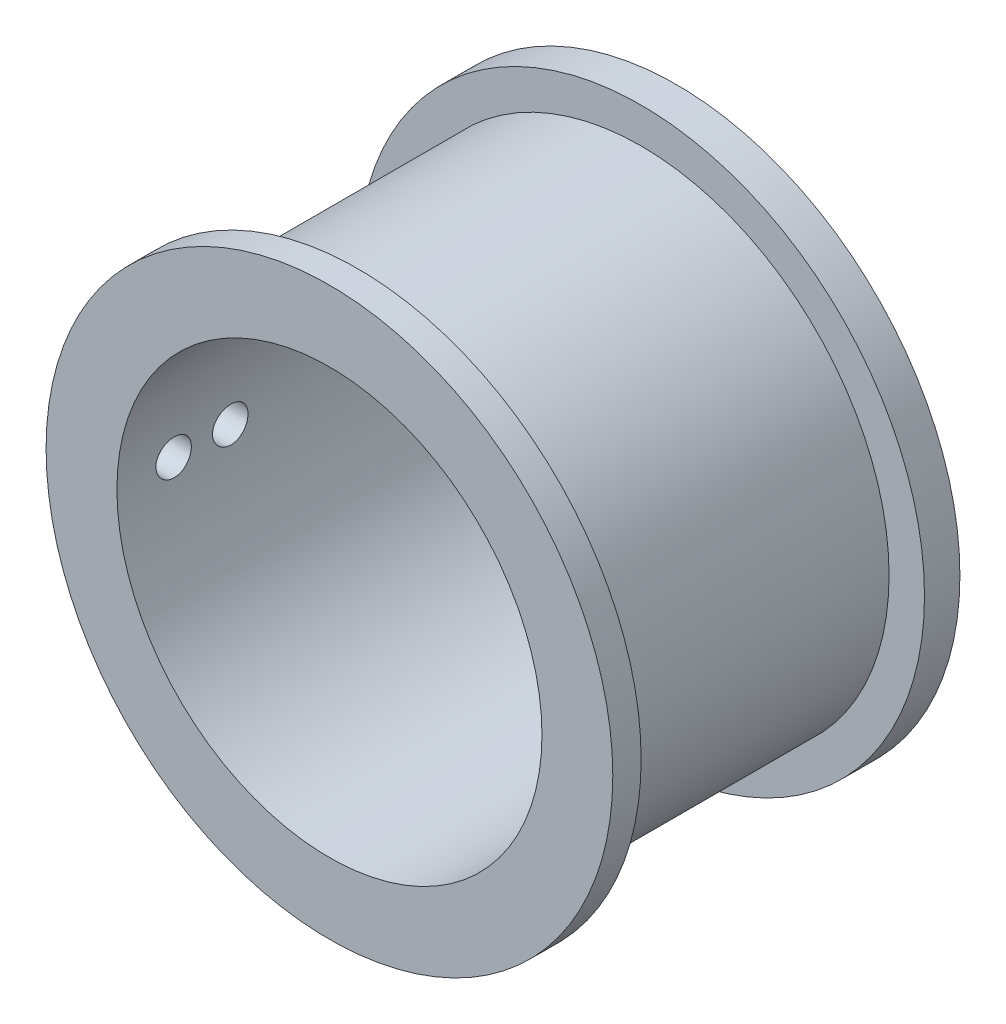
SolidWorks part; units mm, degrees
ref_plane "Front Plane" through (0, 0, 0) normal (0, 0, 1) x (1, 0, 0)
ref_plane "Top Plane" through (0, 0, 0) normal (0, 1, 0) x (1, 0, 0)
ref_plane "Right Plane" through (0, 0, 0) normal (1, 0, 0) x (0, 0, -1)
sketch "Sketch1" plane through (0, 0, 0) normal (0, 0, 1) x (1, 0, 0)
  circle A0 centre (0, 0) radius 25.4
  circle A1 centre (0, 0) radius 8.001 construction
  circle A2 centre (0, -8.001) radius 1.7
  circle A3 centre (0, 8.001) radius 1.7
  circle A4 centre (-6.9291, 4.0005) radius 1.7
  arc A5 (0, 8.001) -> (-6.9291, 4.0005) centre (0, 0) ccw construction
  circle A6 centre (-6.9291, -4.0005) radius 1.7
  circle A7 centre (6.9291, -4.0005) radius 1.7
  circle A8 centre (6.9291, 4.0005) radius 1.7
  dimension "D1" = 50.8
  dimension "D2" = 16.002
  dimension "D9" = 3.4
  dimension "D5" = 60
extrude "Boss-Extrude1" add sketch "Sketch1" along normal blind 3.175
sketch "Sketch4" plane through (0, 0, 3.175) normal (0, 0, 1) x (1, 0, 0)
  circle A0 centre (0, 0) radius 22.225
  circle A1 centre (0, 0) radius 19.05
  circle A2 centre (-6.9291, 4.0005) radius 3.25 construction
  dimension "D1" = 44.45
  dimension "D2" = 38.1
  dimension "D3" = 6.5
extrude "Boss-Extrude2" add sketch "Sketch4" along normal blind 25.4
sketch "Sketch5" plane through (0, 0, 28.575) normal (0, 0, 1) x (1, 0, 0)
  circle A0 centre (0, 0) radius 25.4
  circle A1 centre (0, 0) radius 19.05
  dimension "D1" = 38.1
extrude "Boss-Extrude3" add sketch "Sketch5" along normal blind 2.54
sketch "Sketch6" plane through (0, 0, 0) normal (1, 0, 0) x (0, 0, -1)
  line L0 (-28.575, -25.4) -> (-28.575, 25.4) construction
  circle A0 centre (-26.035, 0) radius 1.5875
  circle A1 centre (-20.955, 0) radius 1.5875
  dimension "D1" = 3.175
  dimension "D2" = 2.54
  dimension "D3" = 5.08
extrude "Cut-Extrude1" cut sketch "Sketch6" against normal through all
